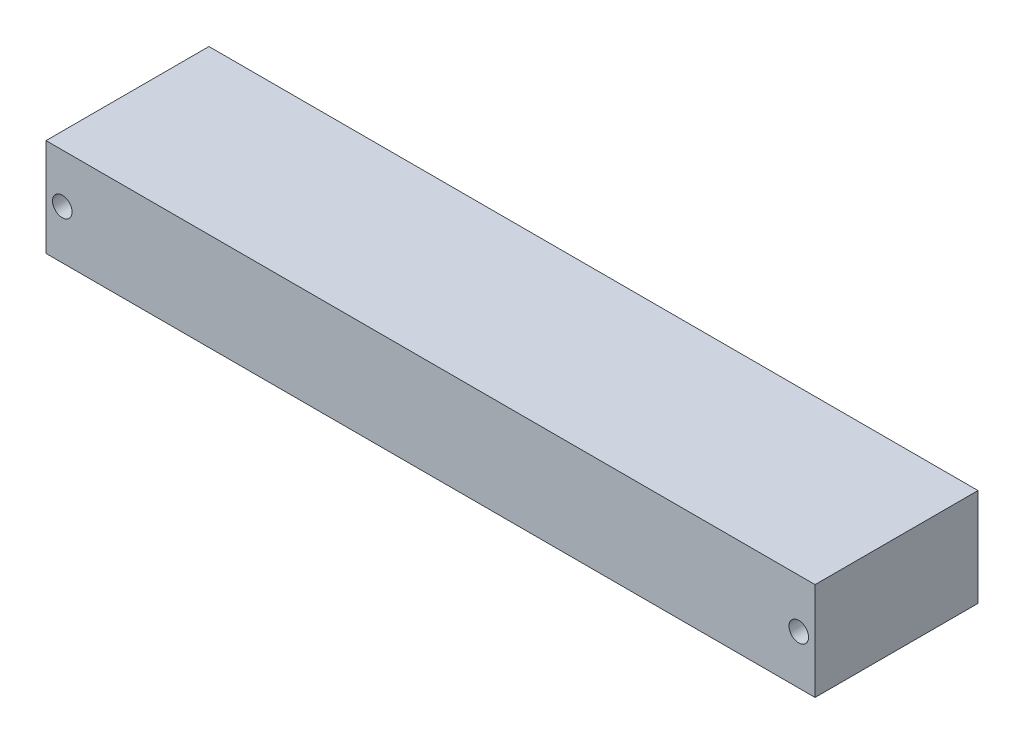
SolidWorks part; units mm, degrees
ref_plane "Front Plane" through (0, 0, 0) normal (0, 0, 1) x (1, 0, 0)
ref_plane "Top Plane" through (0, 0, 0) normal (0, 1, 0) x (1, 0, 0)
ref_plane "Right Plane" through (0, 0, 0) normal (1, 0, 0) x (0, 0, -1)
sketch "Sketch1" plane through (0, 0, 0) normal (0, 1, 0) x (1, 0, 0)
  line L1 (-59, 12.5) -> (59, 12.5)
  line L2 (-59, 12.5) -> (-59, -12.5)
  line L3 (-59, -12.5) -> (59, -12.5)
  line L4 (59, 12.5) -> (59, -12.5)
  line L5 (-59, 12.5) -> (59, -12.5) construction
  line L6 (-59, -12.5) -> (59, 12.5) construction
  point P0 (0, 0)
  dimension "D1" = 25
  dimension "D2" = 118
extrude "Boss-Extrude1" add sketch "Sketch1" along normal blind 15
sketch "Sketch3" plane through (0, 0, 12.5) normal (0, 0, 1) x (1, 0, 0)
  line L0 (-59, 7.5) -> (59, 7.5) construction
  line L1 (-59, 15) -> (-59, 0) construction
  line L2 (59, 15) -> (59, 0) construction
  line L3 (0, 0) -> (0, 15) construction
  line L4 (-59, 15) -> (59, 15) construction
  circle A0 centre (-56.5, 7.5) radius 1.5
  circle A1 centre (56.5, 7.5) radius 1.5
  dimension "D1" = 2.5
  dimension "D2" = 3
extrude "Cut-Extrude1" cut sketch "Sketch3" against normal blind 37
